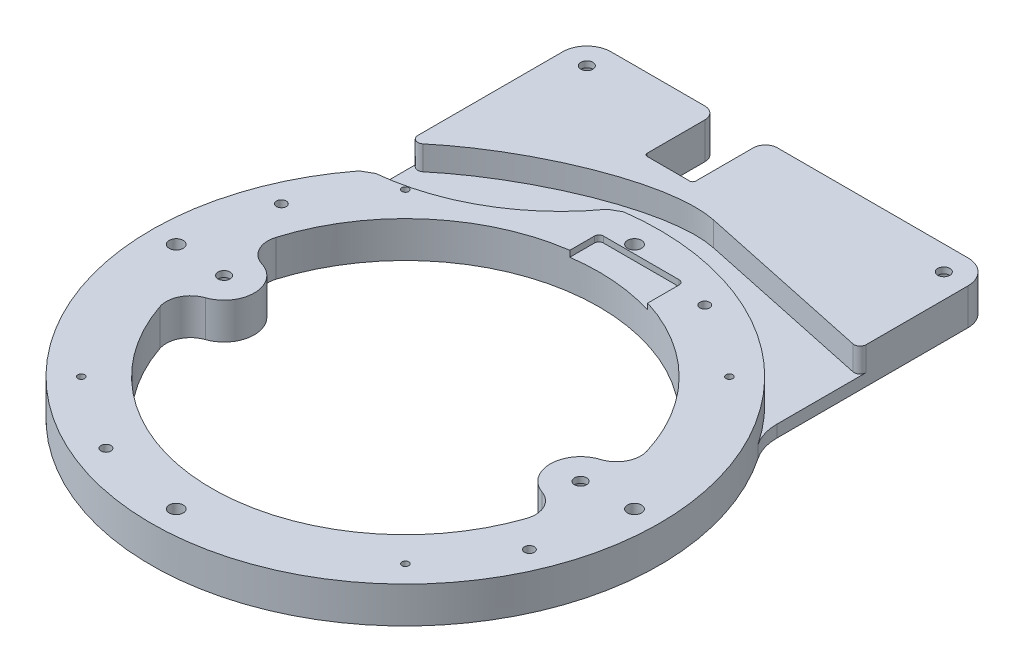
SolidWorks part; units mm, degrees
material "Oak"
ref_plane "Front Plane" through (0, 0, 0) normal (0, 0, 1) x (1, 0, 0)
ref_plane "Top Plane" through (0, 0, 0) normal (0, 1, 0) x (1, 0, 0)
ref_plane "Right Plane" through (0, 0, 0) normal (1, 0, 0) x (0, 0, -1)
sketch "Sketch1" plane through (0, 0, 0) normal (0, 1, 0) x (1, 0, 0)
  circle A0 centre (0, 0) radius 133.35
  dimension "D1" = 266.7
extrude "Boss-Extrude1" add sketch "Sketch1" along normal blind 19.05
sketch "Sketch2" plane through (0, 19.05, 0) normal (0, 1, 0) x (1, 0, 0)
  line L0 (-120.2563, 0) -> (120.2563, 0) construction
  line L1 (85.034, 85.034) -> (-85.034, -85.034) construction
  line L2 (85.034, -85.034) -> (-85.034, 85.034) construction
  line L7 (0, 120.2563) -> (0, -120.2563) construction
  line L8 (46.0201, 0) -> (46.0201, 111.1023) construction
  line L9 (46.0201, 111.1023) -> (0, 111.1023) construction
  line L10 (111.1023, 0) -> (111.1023, -46.0201) construction
  line L11 (111.1023, -46.0201) -> (0, -46.0201) construction
  line L12 (0, -111.1023) -> (-46.0201, -111.1023) construction
  line L13 (-46.0201, -111.1023) -> (-46.0201, 0) construction
  line L14 (-111.1023, 0) -> (-111.1023, 46.0201) construction
  line L15 (-111.1023, 46.0201) -> (0, 46.0201) construction
  circle A0 centre (-120.2563, 0) radius 3.6703
  circle A1 centre (-111.1023, 46.0201) radius 2.5781
  circle A2 centre (120.2563, 0) radius 3.6703
  circle A3 centre (0, -120.2563) radius 3.6703
  circle A4 centre (0, 120.2563) radius 3.6703
  circle A5 centre (111.1023, -46.0201) radius 2.5781
  circle A6 centre (-46.0201, -111.1023) radius 2.5781
  circle A7 centre (46.0201, 111.1023) radius 2.5781
  circle A8 centre (-85.034, -85.034) radius 1.7859
  circle A9 centre (85.034, 85.034) radius 1.7859
  circle A10 centre (-85.034, 85.034) radius 1.7859
  circle A11 centre (85.034, -85.034) radius 1.7859
  point P3 (0, 0)
  point P33 (0, 0)
  dimension "D2" = 7.3406
  dimension "D5" = 5.1562
  dimension "D7" = 3.5719
  dimension "D1" = 240.5126
  dimension "D3" = 46.0201
  dimension "D4" = 111.1023
  dimension "D6" = 45
extrude "Cut-Extrude1" cut sketch "Sketch2" against normal through all
sketch "Sketch3" plane through (0, 19.05, 0) normal (0, 1, 0) x (1, 0, 0)
  line L1 (-106.3625, 80.4316) -> (106.3625, 80.4316) construction
  line L2 (-106.3625, 80.4316) -> (-106.3625, 188.9125)
  line L3 (-93.6625, 201.6125) -> (93.6625, 201.6125)
  line L4 (106.3625, 80.4316) -> (106.3625, 188.9125)
  line L5 (-38.1, 201.6125) -> (-106.3625, 201.6125) construction
  circle A0 centre (0, 0) radius 133.35 construction
  arc A1 (106.3625, 80.4316) -> (-106.3625, 80.4316) centre (0, 0) ccw
  arc A2 (-106.3625, 188.9125) -> (-93.6625, 201.6125) centre (-93.6625, 188.9125) cw
  arc A3 (93.6625, 201.6125) -> (106.3625, 188.9125) centre (93.6625, 188.9125) cw
  dimension "D3" = 12.7
  dimension "D1" = 212.725
extrude "Boss-Extrude2" add sketch "Sketch3" against normal up to surface (19.05 mm away) up to face at (0, 0, -116.586)
fillet "Fillet1" radius 25.4 2 edges at (-106.3625, 9.525, -80.4316) (106.3625, 9.525, -80.4316)
sketch "Sketch4" plane through (0, 19.05, 0) normal (0, 1, 0) x (1, 0, 0)
  line L0 (-14.2875, 163.5125) -> (-36.5125, 163.5125) construction
  line L2 (-38.1, 165.1) -> (-38.1, 195.2625) construction
  line L3 (-12.7, 195.2625) -> (-12.7, 165.1) construction
  line L4 (93.6625, 201.6125) -> (-93.6625, 201.6125) construction
  line L5 (-38.1, 165.1) -> (-38.1, 195.2625)
  line L6 (-12.7, 195.2625) -> (-12.7, 165.1)
  line L7 (-14.2875, 163.5125) -> (-36.5125, 163.5125)
  line L8 (-44.45, 201.6125) -> (-6.35, 201.6125)
  circle A0 centre (-93.6625, 188.9125) radius 3.175
  circle A1 centre (93.6625, 188.9125) radius 3.175
  circle A2 centre (93.5355, -1.5875) radius 3.175
  circle A3 centre (-93.5355, -1.5875) radius 3.175
  circle A4 centre (93.5355, -1.5875) radius 3.175 construction
  circle A5 centre (-93.5355, -1.5875) radius 3.175 construction
  arc A6 (-38.1, 165.1) -> (-36.5125, 163.5125) centre (-36.5125, 165.1) ccw construction
  arc A9 (-14.2875, 163.5125) -> (-12.7, 165.1) centre (-14.2875, 165.1) ccw construction
  arc A10 (-38.1, 195.2625) -> (-44.45, 201.6125) centre (-44.45, 195.2625) ccw
  arc A11 (-6.35, 201.6125) -> (-12.7, 195.2625) centre (-6.35, 195.2625) ccw
  arc A12 (-14.2875, 163.5125) -> (-12.7, 165.1) centre (-14.2875, 165.1) ccw
  arc A13 (-38.1, 165.1) -> (-36.5125, 163.5125) centre (-36.5125, 165.1) ccw
  point P22 (0, 0)
  dimension "D1" = 6.35
extrude "Cut-Extrude2" cut sketch "Sketch4" against normal through all
sketch "Sketch5" plane through (0, 0, 0) normal (0, -1, 0) x (1, 0, 0)
  circle A0 centre (-93.5355, 1.5875) radius 7.9375
  circle A2 centre (-93.6625, -188.9125) radius 7.9375
  circle A3 centre (93.6625, -188.9125) radius 7.9375
  circle A5 centre (93.5355, 1.5875) radius 7.9375
  dimension "D1" = 15.875
extrude "Cut-Extrude3" cut sketch "Sketch5" against normal blind 15.875
sketch "Sketch6" plane through (0, 0, 0) normal (0, -1, 0) x (1, 0, 0)
  arc A0 (-97.2571, -29.3874) -> (97.2571, -29.3874) centre (0, 0) ccw
  arc A1 (-88.8491, -13.58) -> (-88.3371, 16.5872) centre (-93.5355, 1.5875) ccw
  arc A2 (97.2571, -29.3874) -> (88.8491, -13.58) centre (85.0999, -25.714) ccw
  arc A3 (88.3371, 16.5872) -> (88.8491, -13.58) centre (93.5355, 1.5875) ccw
  circle A4 centre (-93.5355, 1.5875) radius 7.9375 construction
  arc A5 (-96.2038, 32.6709) -> (-88.3371, 16.5872) centre (-84.1783, 28.587) ccw
  arc A6 (-88.8491, -13.58) -> (-97.2571, -29.3874) centre (-85.0999, -25.714) ccw
  arc A7 (88.3371, 16.5872) -> (96.2038, 32.6709) centre (84.1783, 28.587) ccw
  arc A8 (96.2038, 32.6709) -> (-96.2038, 32.6709) centre (0, 0) ccw
  circle A9 centre (0, -120.2563) radius 15.875 construction
  circle A10 centre (46.0201, -111.1023) radius 15.875 construction
  circle A11 centre (-93.6625, -188.9125) radius 15.875 construction
  circle A12 centre (93.6625, -188.9125) radius 15.875 construction
  circle A22 centre (-85.034, -85.034) radius 15.875 construction
  circle A23 centre (0, 0) radius 120.65 construction
  dimension "D1" = 203.2
  dimension "D2" = 7.9375
  dimension "D3" = 12.7
  dimension "D4" = 31.75
  dimension "D9" = 19.05
extrude "Cut-Extrude4" cut sketch "Sketch6" against normal through all
sketch "Sketch7" plane through (0, 19.05, 0) normal (0, 1, 0) x (1, 0, 0)
  line L0 (-105.6414, 81.3763) -> (-17.6533, 132.1763) construction
  line L1 (106.3625, 131.5277) -> (9.5861, 152.0982)
  line L2 (106.3625, 88.5449) -> (106.3625, 188.9125) construction
  line L3 (-106.3625, 188.9125) -> (-106.3625, 88.5449) construction
  line L5 (106.3625, 131.5277) -> (110.6805, 74.3777)
  line L7 (-105.6414, 81.3763) -> (-100.1422, 84.5513)
  line L8 (-23.1525, 129.0013) -> (-17.6533, 132.1763)
  line L9 (-106.3625, 105.8328) -> (-110.6805, 74.3777)
  circle A0 centre (0, 0) radius 107.95 construction
  circle A1 centre (0, 0) radius 133.35 construction
  arc A2 (-110.6805, 74.3777) -> (110.6805, 74.3777) centre (0, 0) ccw construction
  arc A3 (110.6805, 74.3777) -> (-17.6533, 132.1763) centre (0, 0) ccw
  arc A4 (-110.6805, 74.3777) -> (-105.6414, 81.3763) centre (0, 0) cw
  arc A7 (-100.1422, 84.5513) -> (-23.1525, 129.0013) centre (-111.1244, 192.4732) ccw
  spline S0 degree 3 poles (9.5861, 152.0982) (-20.2337, 158.4366) (-75.8608, 134.1491) (-106.3625, 105.8328) knots 0 0 0 0 1 1 1 1
  point P23 (-56.8848, 98.5274)
  dimension "D1" = 215.9
  dimension "D2" = 152.4
  dimension "D3" = 78
  dimension "D4" = 57.15
  dimension "D5" = 101.6
  dimension "D6" = 9.525
  dimension "D7" = 88.9
  dimension "D8" = 60
  dimension "D9" = 31.75
extrude "Cut-Extrude5" cut sketch "Sketch7" against normal blind 12.7
fillet "Fillet2" radius 3.175 2 edges at (106.3625, 12.7, -131.5277) (-106.3625, 12.7, -105.8328)
sketch "Sketch8" plane through (0, 19.05, 0) normal (0, 1, 0) x (1, 0, 0)
  line L0 (106.3625, 135.4485) -> (106.3625, 188.9125) construction
  line L1 (27.7812, 115.8875) -> (-11.9062, 115.8875)
  line L2 (30.1625, 113.5063) -> (30.1625, 84.1375)
  line L3 (30.1625, 84.1375) -> (-14.2875, 84.1375)
  line L4 (-14.2875, 113.5063) -> (-14.2875, 84.1375)
  line L5 (93.6625, 201.6125) -> (-6.35, 201.6125) construction
  arc A0 (-11.9062, 115.8875) -> (-14.2875, 113.5063) centre (-11.9063, 113.5063) ccw
  arc A1 (27.7812, 115.8875) -> (30.1625, 113.5063) centre (27.7812, 113.5063) cw
  point P5 (-13.0641, 120.2563)
  point P9 (0, 0)
  point P13 (-14.2875, 115.8875)
  point P16 (30.1625, 115.8875)
  dimension "D5" = 2.3813
  dimension "D1" = 76.2
  dimension "D2" = 44.45
  dimension "D3" = 31.75
  dimension "D4" = 85.725
extrude "Cut-Extrude6" cut sketch "Sketch8" against normal blind 3.175
